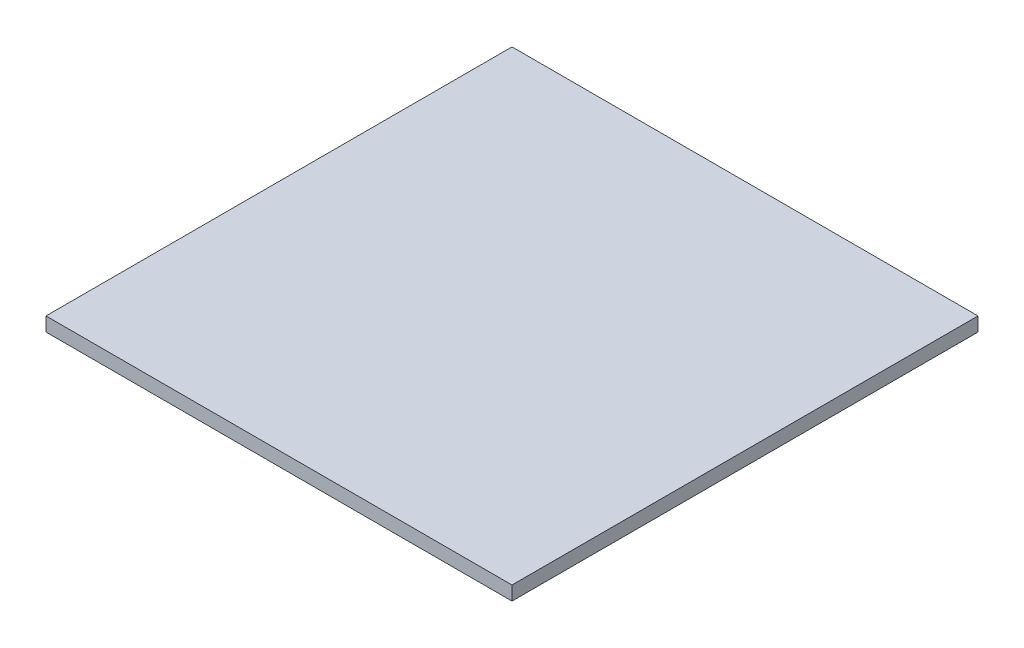
SolidWorks part; units mm, degrees
ref_plane "Front Plane" through (0, 0, 0) normal (0, 0, 1) x (1, 0, 0)
ref_plane "Top Plane" through (0, 0, 0) normal (0, 1, 0) x (1, 0, 0)
ref_plane "Right Plane" through (0, 0, 0) normal (1, 0, 0) x (0, 0, -1)
sketch "Sketch1" plane through (0, 0, 0) normal (0, 1, 0) x (1, 0, 0)
  line L0 (0, 0) -> (200, 0)
  line L1 (200, 0) -> (200, 200)
  line L2 (200, 200) -> (0, 200)
  line L3 (0, 200) -> (0, 0)
  dimension "D1" = 200
  dimension "D2" = 200
extrude "Boss-Extrude1" add sketch "Sketch1" along normal blind 6 contours L1 L2 L3 L0
